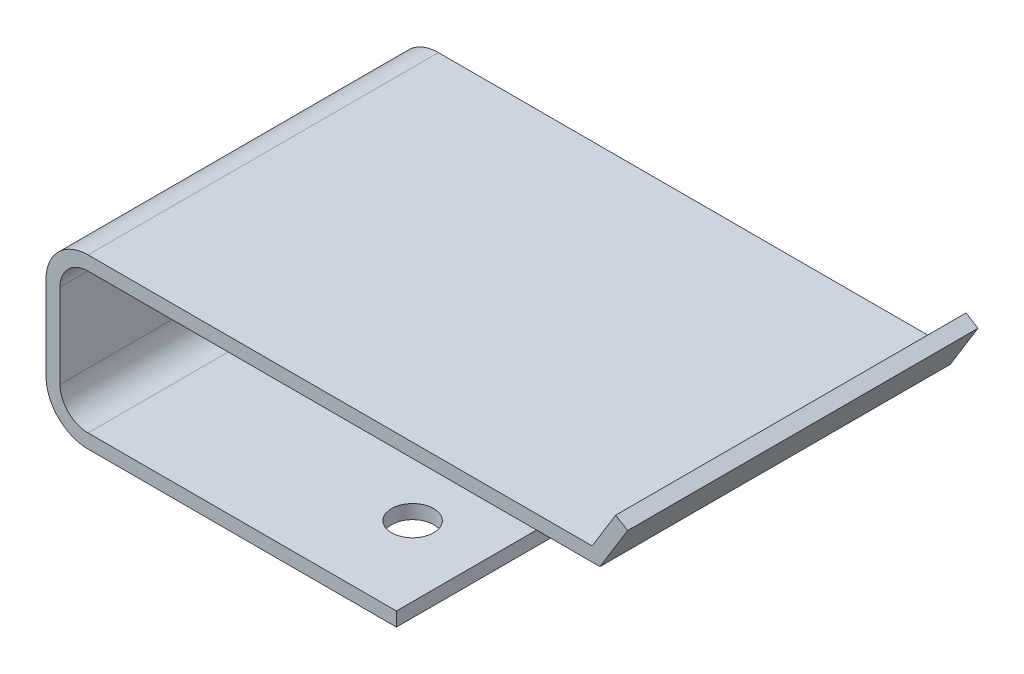
SolidWorks part; units mm, degrees
ref_plane "Plano frontal" through (0, 0, 0) normal (0, 0, 1) x (1, 0, 0)
ref_plane "Plano superior" through (0, 0, 0) normal (0, 1, 0) x (1, 0, 0)
ref_plane "Plano direito" through (0, 0, 0) normal (1, 0, 0) x (0, 0, -1)
sketch "Esboço1" plane through (0, 0, 0) normal (0, 0, 1) x (1, 0, 0)
  line L0 (0, 0) -> (-22, 0)
  line L1 (-25, 3) -> (-25, 9)
  line L2 (-10, 12) -> (13.9646, 12)
  line L3 (13.9646, 12) -> (15.6451, 14.7383)
  line L4 (-22, 12) -> (-10, 12)
  arc A0 (-25, 3) -> (-22, 0) centre (-22, 3) ccw
  arc A1 (-22, 12) -> (-25, 9) centre (-22, 9) ccw
  dimension "D1" = 3
extrude "Extrusão-Fina1" add sketch "Esboço1" along normal blind 25 thin
sketch "Esboço2" plane through (0, 0, 0) normal (0, -1, 0) x (1, 0, 0)
  circle A0 centre (-5, 18.8424) radius 1.5
  circle A1 centre (-5, 3.9046) radius 1.5
extrude "Corte-extrusão1" cut sketch "Esboço2" against normal blind 5
